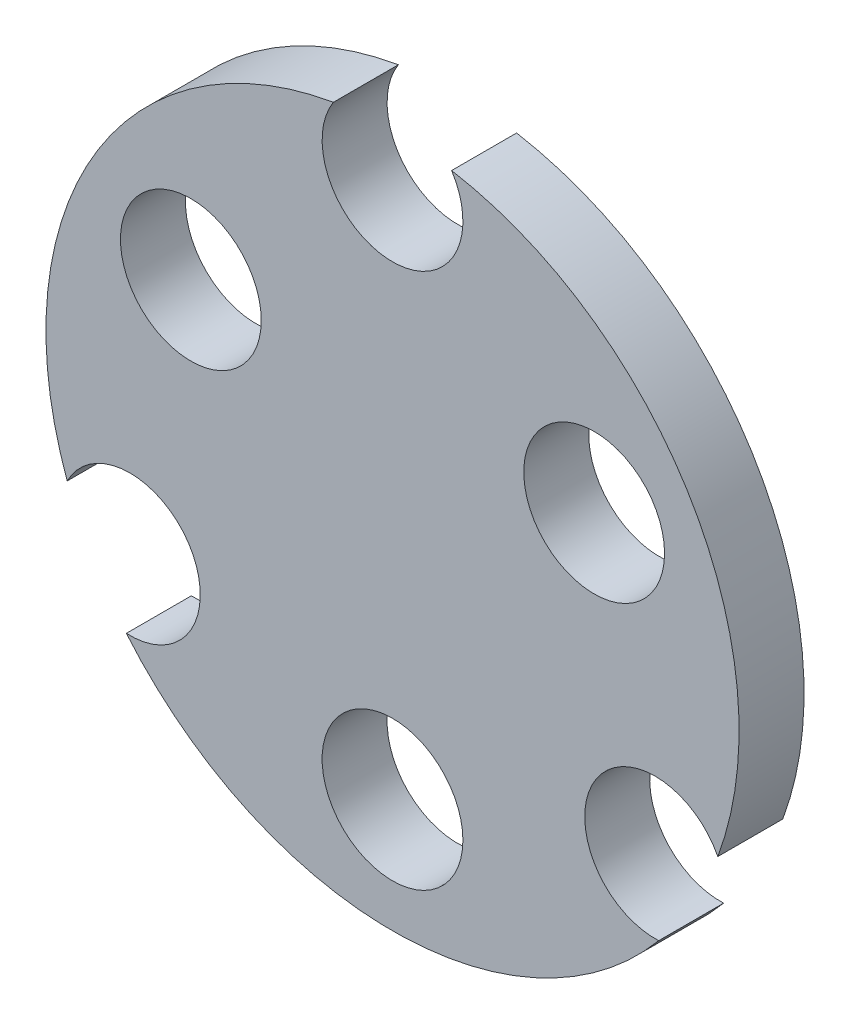
SolidWorks part; units mm, degrees
ref_plane "Plan de face" through (0, 0, 0) normal (0, 0, 1) x (1, 0, 0)
ref_plane "Plan de dessus" through (0, 0, 0) normal (0, 1, 0) x (1, 0, 0)
ref_plane "Plan de droite" through (0, 0, 0) normal (1, 0, 0) x (0, 0, -1)
sketch "Esquisse1" plane through (0, 0, 0) normal (0, 0, 1) x (1, 0, 0)
  line L1 (-10.6244, -7.0011) -> (-8.8744, -7.0011) construction
  line L2 (12.125, -7.0011) -> (10.4994, -4.1854) construction
  line L3 (-10.4994, -4.1854) -> (-12.125, -7.0011) construction
  arc A0 (-12.2881, -10.247) -> (12.2891, -10.2458) centre (0, 0) ccw
  arc A30 (15.0177, -5.5198) -> (12.2891, -10.2458) centre (12.1244, -7) ccw
  arc A31 (-12.2881, -10.247) -> (-15.0177, -5.5197) centre (-12.125, -7.0011) ccw
  arc A32 (-2.7286, 15.7656) -> (2.7286, 15.7656) centre (0, 14) ccw
  arc A33 (-2.7286, 15.7656) -> (-15.0177, -5.5197) centre (0, 0) ccw
  arc A34 (15.0177, -5.5198) -> (2.7286, 15.7656) centre (0, 0) ccw
  point P31 (0, 0)
  dimension "D1" = 32
  dimension "D4" = 6.5
  dimension "D5" = 6.5
  dimension "D8" = 6.5
  dimension "D12" = 24.25
  dimension "D13" = 24.25
extrude "Boss.-Extru.2" add sketch "Esquisse1" along normal blind 3
sketch "Esquisse2" plane through (0, 0, 3) normal (0, 0, 1) x (1, 0, 0)
  line L0 (-12.125, -7.0011) -> (12.1244, -7) construction
  line L1 (12.1244, -7) -> (0, 14) construction
  line L2 (0, 14) -> (-12.125, -7.0011) construction
  line L3 (0, 0) -> (-17.169, 9.9125) construction
  circle A0 centre (-9.3098, 5.375) radius 3.25
  circle A1 centre (9.3098, 5.375) radius 3.25
  circle A2 centre (0, -10.75) radius 3.25
  point P18 (0, 0)
  dimension "D1" = 10.75
  dimension "D2" = 6.5
  dimension "D3" = 3
extrude "Enlèv. mat.-Extru.1" cut sketch "Esquisse2" against normal blind 10
